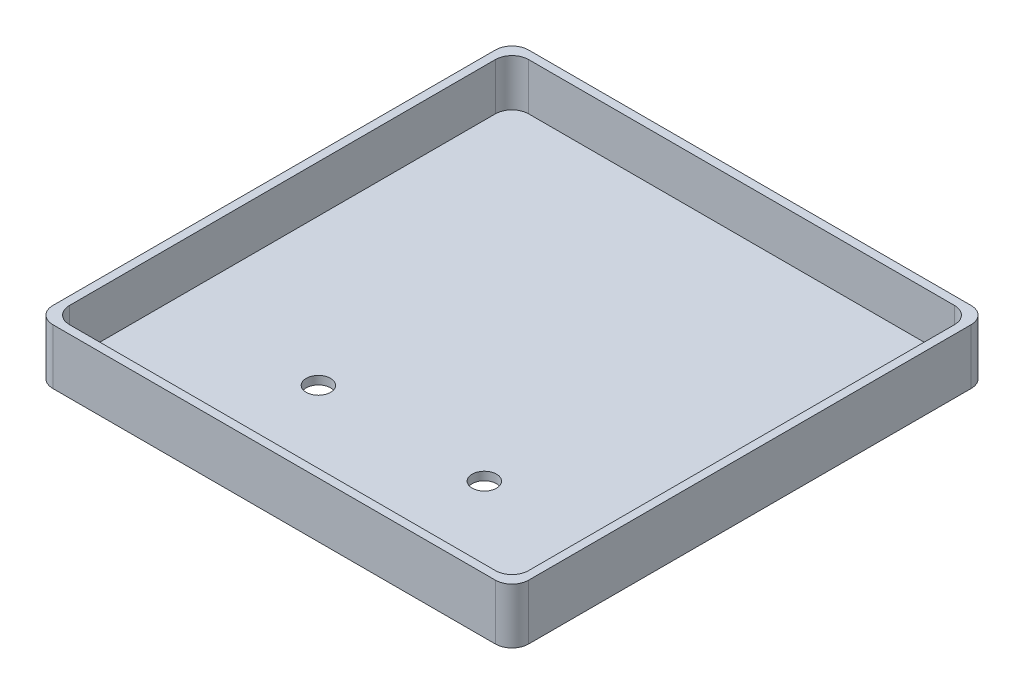
SolidWorks part; units mm, degrees
ref_plane "Спереди" through (0, 0, 0) normal (0, 0, 1) x (1, 0, 0)
ref_plane "Сверху" through (0, 0, 0) normal (0, 1, 0) x (1, 0, 0)
ref_plane "Справа" through (0, 0, 0) normal (1, 0, 0) x (0, 0, -1)
sketch "Эскиз1" plane through (0, 0, 0) normal (0, 1, 0) x (1, 0, 0)
  line L1 (-40, 43) -> (40, 43)
  line L2 (-43, 40) -> (-43, -40)
  line L3 (-40, -43) -> (40, -43)
  line L4 (43, 40) -> (43, -40)
  line L5 (-43, 43) -> (43, -43) construction
  line L6 (-43, -43) -> (43, 43) construction
  arc A0 (-43, -40) -> (-40, -43) centre (-40, -40) ccw
  arc A1 (40, -43) -> (43, -40) centre (40, -40) ccw
  arc A2 (40, 43) -> (43, 40) centre (40, 40) cw
  arc A3 (-40, 43) -> (-43, 40) centre (-40, 40) ccw
  point P0 (0, 0)
  dimension "D1" = 3
extrude "Бобышка-Вытянуть1" add sketch "Эскиз1" along normal blind 10
sketch "Эскиз2" plane through (0, 10, 0) normal (0, 1, 0) x (1, 0, 0)
  line L1 (-38.5, -41.5) -> (38.5, -41.5)
  line L2 (-41.5, -38.5) -> (-41.5, 38.5)
  line L3 (-38.5, 41.5) -> (38.5, 41.5)
  line L4 (41.5, -38.5) -> (41.5, 38.5)
  line L5 (-41.5, -41.5) -> (41.5, 41.5) construction
  line L6 (-41.5, 41.5) -> (41.5, -41.5) construction
  arc A0 (-38.5, -41.5) -> (-41.5, -38.5) centre (-38.5, -38.5) cw
  arc A1 (38.5, -41.5) -> (41.5, -38.5) centre (38.5, -38.5) ccw
  arc A2 (38.5, 41.5) -> (41.5, 38.5) centre (38.5, 38.5) cw
  arc A3 (-41.5, 38.5) -> (-38.5, 41.5) centre (-38.5, 38.5) cw
  point P0 (0, 0)
  dimension "D1" = 3
extrude "Вырез-Вытянуть1" cut sketch "Эскиз2" against normal blind 8.5
sketch "Эскиз3" plane through (0, 0, 0) normal (0, -1, 0) x (1, 0, 0)
  line L0 (0, 45.2618) -> (0, -45.9021) construction
  circle A0 centre (-15, 20) radius 2.2
  circle A1 centre (15, 20) radius 2.2
extrude "Вырез-Вытянуть2" cut sketch "Эскиз3" against normal through all
